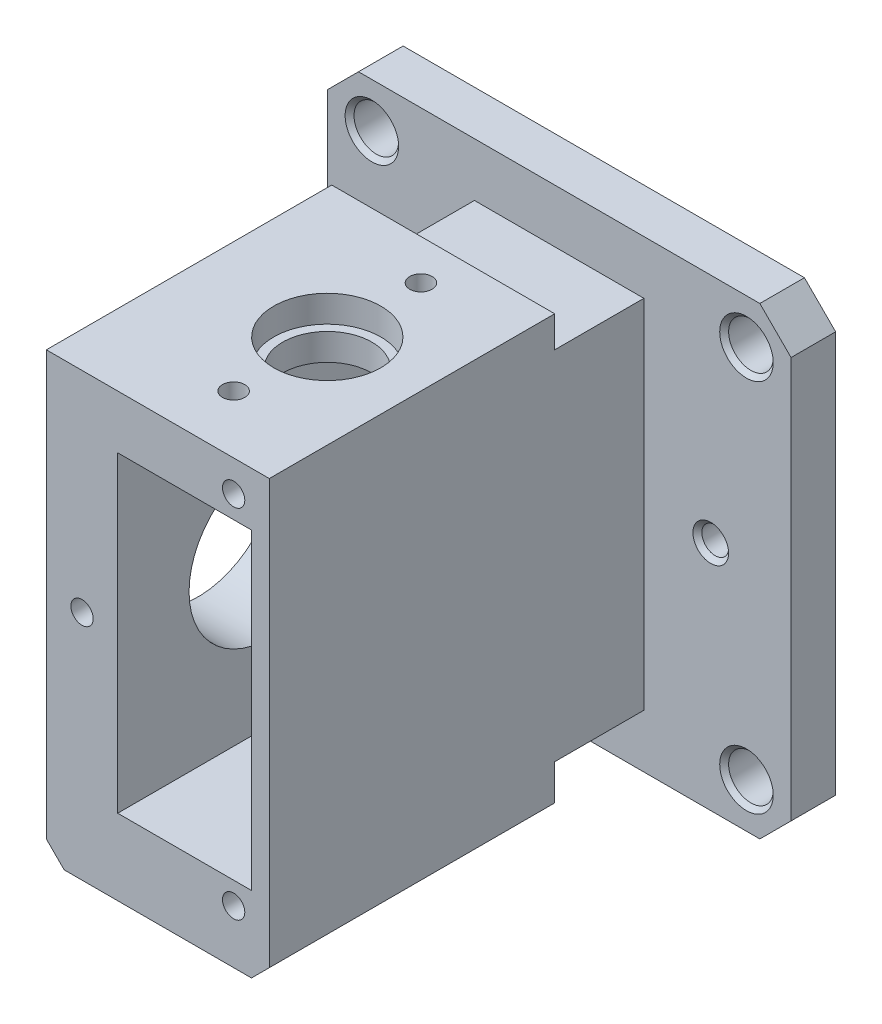
SolidWorks part; units mm, degrees
material "Сталь"
ref_plane "Спереди" through (0, 0, 0) normal (0, 0, 1) x (1, 0, 0)
ref_plane "Сверху" through (0, 0, 0) normal (0, 1, 0) x (1, 0, 0)
ref_plane "Справа" through (0, 0, 0) normal (1, 0, 0) x (0, 0, -1)
sketch "Эскиз1" plane through (0, 0, 0) normal (0, 0, 1) x (1, 0, 0)
  line L1 (-26, -26) -> (26, -26)
  line L2 (-26, -26) -> (-26, 26)
  line L3 (-26, 26) -> (26, 26)
  line L4 (26, -26) -> (26, 26)
  line L5 (-26, -26) -> (26, 26) construction
  line L6 (-26, 26) -> (26, -26) construction
  point P0 (0, 0)
  dimension "D1" = 52
extrude "Бобышка-Вытянуть1" add sketch "Эскиз1" along normal blind 5
sketch "Эскиз2" plane through (0, 0, 5) normal (0, 0, 1) x (1, 0, 0)
  line L1 (-21, -21) -> (21, -21)
  line L2 (-21, -21) -> (-21, 21)
  line L3 (-21, 21) -> (21, 21)
  line L4 (21, -21) -> (21, 21)
  line L5 (-21, -21) -> (21, 21) construction
  line L6 (-21, 21) -> (21, -21) construction
  circle A0 centre (21, 21) radius 2.5
  circle A1 centre (21, -21) radius 2.5
  circle A2 centre (-21, -21) radius 2.5
  circle A3 centre (-21, 21) radius 2.5
  point P0 (0, 0)
  dimension "D2" = 5
  dimension "D1" = 42
extrude "Вырез-Вытянуть1" cut sketch "Эскиз2" against normal through all contours L3 A3 L2 | L4 A0 L3 | L3 A0 L4 | L2 A3 L3 | L2 A2 L1 | L1 A2 L2 | L1 A1 L4 | L4 A1 L1
chamfer "Фаска1" distance 3.5 angle 45 4 edges at (-26, 26, 2.5) (26, 26, 2.5) (26, -26, 2.5) (-26, -26, 2.5)
chamfer "Фаска2" distance 0.5 angle 45 4 edges at (23.5, -21, 5) (23.5, 21, 5) (-18.5, 21, 5) (-18.5, -21, 5)
sketch "Эскиз3" plane through (0, 0, 5) normal (0, 0, 1) x (1, 0, 0)
  line L0 (-26, 0) -> (26, 0) construction
  line L1 (-26, 22.5) -> (-26, -22.5) construction
  line L2 (26, -22.5) -> (26, 22.5) construction
  line L4 (9.5, -20) -> (-9.5, -20)
  line L5 (9.5, -20) -> (9.5, 20)
  line L6 (9.5, 20) -> (-9.5, 20)
  line L7 (-9.5, -20) -> (-9.5, 20)
  line L8 (9.5, -20) -> (-9.5, 20) construction
  line L9 (9.5, 20) -> (-9.5, -20) construction
  point P6 (0, 0)
  dimension "D1" = 19
  dimension "D2" = 40
extrude "Бобышка-Вытянуть2" add sketch "Эскиз3" along normal blind 42
sketch "Эскиз6" plane through (0, 0, 47) normal (0, 0, 1) x (1, 0, 0)
  line L1 (-7.5, -17.5) -> (7.5, -17.5)
  line L2 (-7.5, -17.5) -> (-7.5, 17.5)
  line L3 (-7.5, 17.5) -> (7.5, 17.5)
  line L4 (7.5, -17.5) -> (7.5, 17.5)
  line L5 (-7.5, -17.5) -> (7.5, 17.5) construction
  line L6 (-7.5, 17.5) -> (7.5, -17.5) construction
  point P0 (0, 0)
  dimension "D1" = 15
  dimension "D2" = 35
sketch "Эскиз4" plane through (0, 0, 47) normal (0, 0, 1) x (1, 0, 0)
  line L0 (22.5, 26) -> (-22.5, 26) construction
  line L1 (-15.5, -26) -> (9.5, -26)
  line L2 (-15.5, -26) -> (-15.5, 26)
  line L3 (-15.5, 26) -> (9.5, 26)
  line L4 (9.5, -26) -> (9.5, 26)
  line L5 (-15.5, -26) -> (9.5, 26) construction
  line L6 (-15.5, 26) -> (9.5, -26) construction
  line L7 (9.5, -20) -> (9.5, 20) construction
  point P0 (-3, 0)
  dimension "D1" = 25
extrude "Бобышка-Вытянуть3" add sketch "Эскиз4" against normal blind 32
extrude "Вырез-Вытянуть2" cut sketch "Эскиз6" against normal through all
sketch "Эскиз7" plane through (-15.5, 0, 0) normal (-1, 0, 0) x (0, 0, 1)
  line L0 (15, 26) -> (15, -26) construction
  circle A0 centre (30, 0) radius 9
  dimension "D1" = 18
  dimension "D2" = 15
extrude "Вырез-Вытянуть3" cut sketch "Эскиз7" against normal up to next
sketch "Эскиз8" plane through (-15.5, 0, 0) normal (-1, 0, 0) x (0, 0, 1)
  line L1 (21, 11) -> (39, 11) construction
  line L2 (21, 11) -> (21, -11) construction
  line L3 (21, -11) -> (39, -11) construction
  line L4 (39, 11) -> (39, -11) construction
  line L5 (21, 11) -> (39, -11) construction
  line L6 (21, -11) -> (39, 11) construction
  point P0 (30, 0)
  dimension "D1" = 18
  dimension "D2" = 22
hole_wizard "Отверстие обработанное метчиком M3x0.51" positions "Трехмерный эскиз1" profile "Эскиз9" tap size "M3x0.5" standard "Ansi Metric"
sketch3d "Трехмерный эскиз1"
  point P0 (-15.5, 11, 39)
  point P3 (-15.5, -11, 39)
  point P6 (-15.5, -11, 21)
  point P9 (-15.5, 11, 21)
sketch "Эскиз9" plane through (-15.5, 11, 39) normal (0, 1, 0) x (0, 0, 1)
  line L0 (0, 0) -> (0, 6.2511)
  line L1 (0, 6.2511) -> (1.25, 5.5)
  line L2 (1.25, 5.5) -> (1.25, 0)
  line L5 (1.25, 0) -> (0, 0)
  line L10 (0, 6.2511) -> (-1.25, 5.5) construction
  line L11 (0, -6.35) -> (0, 107.95) construction
  dimension "Диаметр сверла" = 2.5
  dimension "Глубина сверла" = 5.5
  dimension "Угол заточки сверла" = 118
cosmetic thread "Отверстие резьбы1" parameters "D1"=4, "D2"=3
cosmetic thread "Отверстие резьбы2" parameters "D1"=4, "D2"=3
cosmetic thread "Отверстие резьбы3" parameters "D1"=4, "D2"=3
cosmetic thread "Отверстие резьбы4" parameters "D1"=4, "D2"=3
chamfer "Фаска3" distance 2 angle 45 4 edges at (9.5, -26, 31) (9.5, 26, 31) (-15.5, 26, 31) (-15.5, -26, 31)
sketch "Эскиз11" plane through (0, 0, 47) normal (0, 0, 1) x (1, 0, 0)
  point P0 (5.5, 20)
  point P1 (-11.5, 0)
  point P3 (5.5, -20)
hole_wizard "Отверстие обработанное метчиком M3x0.52" positions "Трехмерный эскиз3" profile "Эскиз12" tap size "M3x0.5" standard "Ansi Metric"
sketch3d "Трехмерный эскиз3"
  point P0 (5.5, 20, 47)
  point P3 (-11.5, 0, 47)
  point P6 (5.5, -20, 47)
sketch "Эскиз12" plane through (5.5, 20, 47) normal (1, 0, 0) x (0, -1, 0)
  line L0 (0, 0) -> (0, 6.2511)
  line L1 (0, 6.2511) -> (1.25, 5.5)
  line L2 (1.25, 5.5) -> (1.25, 0)
  line L5 (1.25, 0) -> (0, 0)
  line L10 (0, 6.2511) -> (-1.25, 5.5) construction
  line L11 (0, -6.35) -> (0, 107.95) construction
  dimension "Диаметр сверла" = 2.5
  dimension "Глубина сверла" = 5.5
  dimension "Угол заточки сверла" = 118
cosmetic thread "Отверстие резьбы5" parameters "D1"=4, "D2"=3
cosmetic thread "Отверстие резьбы6" parameters "D1"=4, "D2"=3
cosmetic thread "Отверстие резьбы7" parameters "D1"=4, "D2"=3
sketch "Эскиз13" plane through (0, -26, 0) normal (0, -1, 0) x (-1, 0, 0)
  line L0 (26, 0) -> (26, -5) construction
  line L1 (22.5, 0) -> (-22.5, 0) construction
  circle A0 centre (1, -30) radius 3.1
  dimension "D3" = 6.2
  dimension "D1" = 25
  dimension "D2" = 30
extrude "Вырез-Вытянуть4" cut sketch "Эскиз13" against normal blind 7
sketch "Эскиз14" plane through (0, -19, 0) normal (0, -1, 0) x (1, 0, 0)
  circle A0 centre (-1, 30) radius 1.55
  dimension "D1" = 3.1
extrude "Вырез-Вытянуть5" cut sketch "Эскиз14" against normal up to next
chamfer "Фаска4" distance 1 angle 45 1 edges at (-1, -26, 26.9)
sketch "Эскиз15" plane through (0, 26, 0) normal (0, 1, 0) x (1, 0, 0)
  line L1 (-15.5, -47) -> (9.5, -47)
  line L2 (-15.5, -47) -> (-15.5, -15)
  line L3 (-15.5, -15) -> (9.5, -15)
  line L4 (9.5, -47) -> (9.5, -15)
extrude "Вырез-Вытянуть6" cut sketch "Эскиз15" against normal blind 2.5
sketch "Эскиз16" plane through (0, 23.5, 0) normal (0, 1, 0) x (1, 0, 0)
  circle A0 centre (-1, -30) radius 6
  dimension "D1" = 12
extrude "Вырез-Вытянуть7" cut sketch "Эскиз16" against normal blind 3
sketch "Эскиз17" plane through (0, 20.5, 0) normal (0, 1, 0) x (1, 0, 0)
  circle A0 centre (-1, -30) radius 5
  dimension "D1" = 10
extrude "Вырез-Вытянуть8" cut sketch "Эскиз17" against normal up to next
sketch "Эскиз18" plane through (0, 23.5, 0) normal (0, 1, 0) x (1, 0, 0)
  line L0 (-1, -30) -> (-1, -47) construction
  line L1 (-15.5, -47) -> (9.5, -47) construction
  line L2 (-1, -30) -> (-1, -15) construction
  line L3 (9.5, -15) -> (-15.5, -15) construction
  point P5 (-1, -40.5)
  point P9 (-1, -19.5)
  dimension "D1" = 10.5
  dimension "D2" = 10.5
hole_wizard "Отверстие обработанное метчиком M3x0.53" positions "Трехмерный эскиз4" profile "Эскиз19" tap size "M3x0.5" standard "Ansi Metric"
sketch3d "Трехмерный эскиз4"
  point P0 (-1, 23.5, 40.5)
  point P3 (-1, 23.5, 19.5)
sketch "Эскиз19" plane through (-1, 23.5, 40.5) normal (1, 0, 0) x (0, 0, 1)
  line L0 (0, 0) -> (0, 5.2511)
  line L1 (0, 5.2511) -> (1.25, 4.5)
  line L2 (1.25, 4.5) -> (1.25, 0)
  line L5 (1.25, 0) -> (0, 0)
  line L10 (0, 5.2511) -> (-1.25, 4.5) construction
  line L11 (0, -6.35) -> (0, 107.95) construction
  dimension "Диаметр сверла" = 2.5
  dimension "Глубина сверла" = 4.5
  dimension "Угол заточки сверла" = 118
cosmetic thread "Отверстие резьбы8" parameters "D1"=3.5, "D2"=3
cosmetic thread "Отверстие резьбы9" parameters "D1"=3.5, "D2"=3
sketch "Эскиз20" plane through (0, 0, 0) normal (0, 0, -1) x (-1, 0, 0)
  line L0 (-26, 0) -> (26, 0) construction
  line L1 (-26, -22.5) -> (-26, 22.5) construction
  line L2 (26, 22.5) -> (26, -22.5) construction
  circle A0 centre (-17, 0) radius 1.5
  circle A1 centre (17, 0) radius 1.5
  dimension "D1" = 3
  dimension "D2" = 9
  dimension "D3" = 9
extrude "Вырез-Вытянуть9" cut sketch "Эскиз20" against normal up to next
chamfer "Фаска5" distance 0.5 angle 45 2 edges at (15.5, 0, 5) (-18.5, 0, 5)
